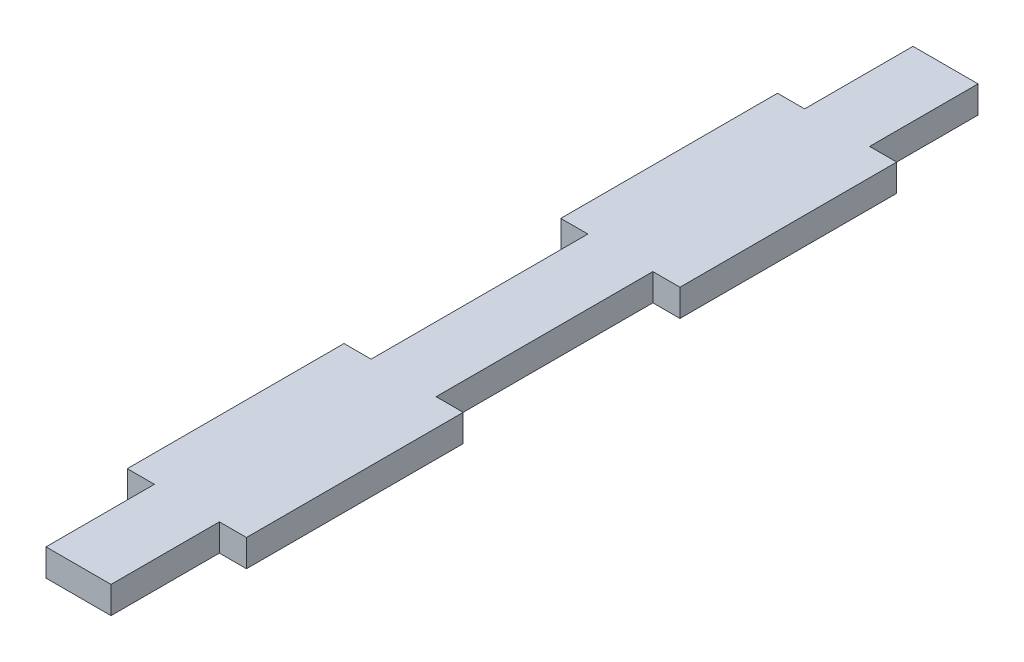
SolidWorks part; units mm, degrees
ref_plane "Front Plane" through (0, 0, 0) normal (0, 0, 1) x (1, 0, 0)
ref_plane "Top Plane" through (0, 0, 0) normal (0, 1, 0) x (1, 0, 0)
ref_plane "Right Plane" through (0, 0, 0) normal (1, 0, 0) x (0, 0, -1)
sketch "Sketch1" plane through (0, 0, 0) normal (0, 1, 0) x (1, 0, 0)
  line L0 (0, 88.9) -> (0, 101.6)
  line L1 (0, 0) -> (7.62, 0)
  line L2 (0, 0) -> (0, 12.7)
  line L3 (0, 101.6) -> (7.62, 101.6)
  line L4 (7.62, 0) -> (7.62, 12.7)
  line L5 (0, 101.6) -> (-3.175, 101.6)
  line L6 (0, 101.6) -> (0, 88.9)
  line L7 (0, 88.9) -> (-3.175, 88.9)
  line L8 (-3.175, 101.6) -> (-3.175, 88.9)
  line L9 (7.62, 101.6) -> (10.795, 101.6)
  line L10 (7.62, 101.6) -> (7.62, 88.9)
  line L11 (7.62, 88.9) -> (10.795, 88.9)
  line L12 (10.795, 101.6) -> (10.795, 88.9)
  line L13 (7.62, 0) -> (10.795, 0)
  line L14 (7.62, 0) -> (7.62, 12.7)
  line L15 (7.62, 12.7) -> (10.795, 12.7)
  line L16 (10.795, 0) -> (10.795, 12.7)
  line L17 (0, 0) -> (-3.175, 0)
  line L18 (0, 0) -> (0, 12.7)
  line L19 (0, 12.7) -> (-3.175, 12.7)
  line L20 (-3.175, 0) -> (-3.175, 12.7)
  line L21 (7.62, 38.1) -> (10.795, 38.1)
  line L22 (7.62, 38.1) -> (7.62, 63.5)
  line L23 (7.62, 63.5) -> (10.795, 63.5)
  line L24 (10.795, 38.1) -> (10.795, 63.5)
  line L25 (0, 63.5) -> (-3.175, 63.5)
  line L26 (0, 63.5) -> (0, 38.1)
  line L27 (0, 38.1) -> (-3.175, 38.1)
  line L28 (-3.175, 63.5) -> (-3.175, 38.1)
  line L29 (-3.175, 88.9) -> (0, 88.9)
  line L30 (-3.175, 88.9) -> (-3.175, 63.5)
  line L31 (-3.175, 63.5) -> (0, 63.5)
  line L33 (10.795, 88.9) -> (7.62, 88.9)
  line L34 (10.795, 88.9) -> (10.795, 63.5)
  line L35 (10.795, 63.5) -> (7.62, 63.5)
  line L37 (-3.175, 12.7) -> (0, 12.7)
  line L38 (-3.175, 12.7) -> (-3.175, 38.1)
  line L39 (-3.175, 38.1) -> (0, 38.1)
  line L41 (7.62, 38.1) -> (10.795, 38.1)
  line L43 (7.62, 12.7) -> (10.795, 12.7)
  line L44 (10.795, 38.1) -> (10.795, 12.7)
  line L45 (7.62, 88.9) -> (7.62, 101.6)
  line L46 (0, 38.1) -> (0, 63.5)
  line L47 (7.62, 38.1) -> (7.62, 63.5)
  point P25 (9.2075, 0)
  dimension "D1" = 7.62
  dimension "D2" = 101.6
  dimension "D3" = 12.7
  dimension "D4" = 12.7
  dimension "D5" = 25.4
  dimension "D6" = 25.4
  dimension "D7" = 25.4
  dimension "D8" = 25.4
  dimension "D9" = 3.175
  dimension "D10" = 3.175
  dimension "D11" = 3.175
  dimension "D12" = 3.175
  dimension "D13" = 3.175
  dimension "D14" = 3.175
  dimension "D15" = 12.7
  dimension "D16" = 12.7
extrude "Boss-Extrude2" add sketch "Sketch1" along normal blind 3.175 contours L44 L21 L22 L23 L34 L11 L10 L3 L0 L7 L30 L25 L26 L27 L38 L19 L2 L1 L4 L15
